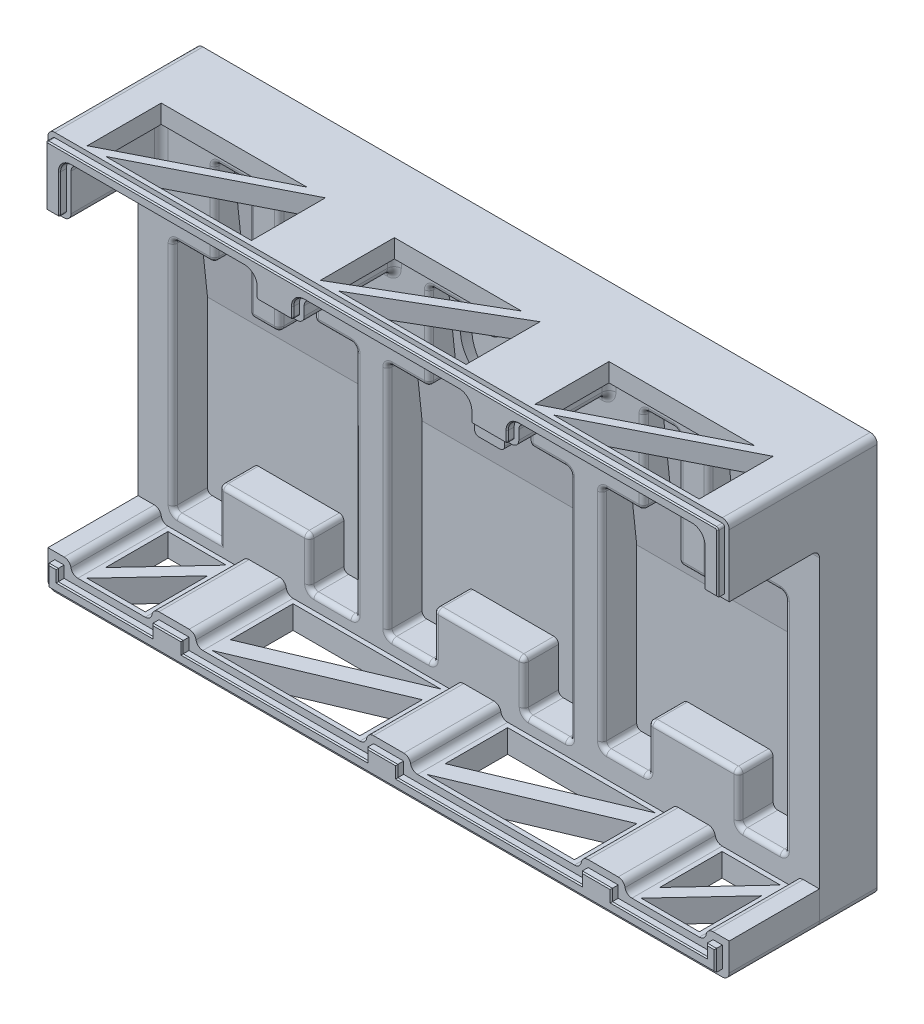
SolidWorks part; units mm, degrees
material "PP generico"
ref_plane "Piano frontale" through (0, 0, 0) normal (0, 0, 1) x (1, 0, 0)
ref_plane "Piano superiore" through (0, 0, 0) normal (0, 1, 0) x (1, 0, 0)
ref_plane "Piano destro" through (0, 0, 0) normal (1, 0, 0) x (0, 0, -1)
sketch "Schizzo1" plane through (0, 0, 0) normal (0, 0, 1) x (1, 0, 0)
  line L1 (-147.3, 86) -> (147.3, 86)
  line L2 (-147.3, 86) -> (-147.3, -86)
  line L3 (-147.3, -86) -> (147.3, -86)
  line L4 (147.3, 86) -> (147.3, -86)
  dimension "D1" = 294.6
  dimension "D2" = 172
  dimension "D3" = 147.3
  dimension "D4" = 86
extrude "Estrusione-Estrusione1" add sketch "Schizzo1" along normal blind 10 contours L1 L4 L3 L2
sketch "Schizzo2" plane through (0, 0, 10) normal (0, 0, 1) x (1, 0, 0)
  line L0 (-73.3, -70) -> (-53.3, -70)
  line L1 (-147.3, 86) -> (147.3, 86)
  line L2 (-147.3, 86) -> (-147.3, -86)
  line L3 (-6.3232, -86) -> (147.3, -86)
  line L4 (147.3, 86) -> (147.3, -86)
  line L9 (-114.3, 70) -> (-99.3, 70)
  line L10 (-132.3, 32) -> (-132.3, -70)
  line L11 (-132.3, -70) -> (-112.3, -70)
  line L12 (-53.3, 32) -> (-53.3, -70)
  line L14 (-39.5, 32) -> (-39.5, -69.8088)
  line L15 (-39.5, -69.8088) -> (-19.5, -69.8088)
  line L16 (39.5, 32) -> (39.5, -69.8088)
  line L18 (53.3, 32) -> (53.3, -65.4933)
  line L19 (53.3, -65.4933) -> (73.3, -65.4933)
  line L20 (132.3, 32) -> (132.3, -65.4933)
  line L21 (-112.3, -49) -> (-73.3, -49)
  line L22 (-112.3, -49) -> (-112.3, -70)
  line L24 (-73.3, -49) -> (-73.3, -70)
  line L25 (19.5, -69.8088) -> (39.5, -69.8088)
  line L26 (-19.5, -48.8088) -> (19.5, -48.8088)
  line L27 (-19.5, -48.8088) -> (-19.5, -69.8088)
  line L29 (19.5, -48.8088) -> (19.5, -69.8088)
  line L30 (73.3, -44.4933) -> (112.3, -44.4933)
  line L31 (73.3, -44.4933) -> (73.3, -65.4933)
  line L33 (112.3, -44.4933) -> (112.3, -65.4933)
  line L34 (112.3, -65.4933) -> (132.3, -65.4933)
  line L35 (-86.3, 70) -> (-71.3, 70)
  line L38 (-132.3, 32) -> (-114.3, 32)
  line L39 (-114.3, 70) -> (-114.3, 32)
  line L42 (-53.3, 32) -> (-71.3, 32)
  line L43 (-71.3, 70) -> (-71.3, 32)
  line L45 (-99.3, 70) -> (-99.3, 20)
  line L46 (-99.3, 20) -> (-86.3, 20)
  line L47 (-86.3, 70) -> (-86.3, 20)
  line L48 (-21.5, 70) -> (-21.5, 32)
  line L49 (-39.5, 32) -> (-21.5, 32)
  line L50 (-21.5, 70) -> (-6.5, 70)
  line L51 (-6.5, 70) -> (-6.5, 20)
  line L52 (6.5, 70) -> (6.5, 20)
  line L53 (6.5, 70) -> (21.5, 70)
  line L54 (21.5, 70) -> (21.5, 32)
  line L55 (39.5, 32) -> (21.5, 32)
  line L56 (-6.5, 20) -> (6.5, 20)
  line L57 (71.3, 70) -> (71.3, 32)
  line L58 (53.3, 32) -> (71.3, 32)
  line L59 (71.3, 70) -> (86.3, 70)
  line L60 (86.3, 70) -> (86.3, 20)
  line L61 (99.3, 70) -> (99.3, 20)
  line L62 (99.3, 70) -> (114.3, 70)
  line L63 (114.3, 70) -> (114.3, 32)
  line L64 (132.3, 32) -> (114.3, 32)
  line L65 (86.3, 20) -> (99.3, 20)
  dimension "D3" = 15
  dimension "D4" = 13.8
  dimension "D5" = 140
  dimension "D6" = 38
  dimension "D7" = 38
  dimension "D8" = 20
  dimension "D9" = 20
  dimension "D10" = 21
  dimension "D11" = 20
  dimension "D12" = 20
  dimension "D13" = 16
  dimension "D16" = 20
  dimension "D17" = 20
  dimension "D18" = 21
  dimension "D19" = 21
  dimension "D20" = 18
  dimension "D21" = 18
  dimension "D22" = 15
  dimension "D23" = 15
  dimension "D24" = 50
  dimension "D25" = 3
extrude "Estrusione-Estrusione2" add sketch "Schizzo2" along normal blind 15
sketch "Schizzo4" plane through (132.3, 0, 0) normal (-1, 0, 0) x (0, 0, 1)
  line L0 (10, 70) -> (10, 3.34)
  line L1 (10, 32) -> (10, -65.4933) construction
  line L2 (10, 3.34) -> (17.12, 70)
  line L4 (17.12, 70) -> (10, 70)
  dimension "D3" = 68.8333
extrude "Estrusione-Estrusione3" add sketch "Schizzo4" along normal up to surface (264.6 mm away) up to face at (-132.3, -19, 17.5)
sketch "Schizzo5" plane through (0, 0, 25) normal (0, 0, 1) x (1, 0, 0)
  line L0 (-147.3, 86) -> (-147.3, 56)
  line L1 (-147.3, 86) -> (-147.3, -86) construction
  line L2 (-147.3, 56) -> (-137.3, 56)
  line L3 (-137.3, 56) -> (-137.3, 78)
  line L4 (-137.3, 78) -> (-56.3, 78)
  line L5 (-56.3, 78) -> (-56.3, 68)
  line L6 (-56.3, 68) -> (-36.5, 68)
  line L7 (-36.5, 68) -> (-36.5, 78)
  line L8 (-36.5, 78) -> (36.5, 78)
  line L9 (36.5, 78) -> (36.5, 68)
  line L10 (36.5, 68) -> (56.3, 68)
  line L11 (56.3, 68) -> (56.3, 78)
  line L12 (56.3, 78) -> (137.3, 78)
  line L13 (137.3, 78) -> (137.3, 56)
  line L14 (137.3, 56) -> (147.3, 56)
  line L15 (147.3, -86) -> (147.3, 86) construction
  line L16 (147.3, 56) -> (147.3, 86)
  line L17 (147.3, 86) -> (-147.3, 86)
  line L18 (-21.5, 70) -> (-21.5, 32) construction
  line L19 (-71.3, 32) -> (-71.3, 70) construction
  line L20 (21.5, 32) -> (21.5, 70) construction
  line L22 (71.3, 70) -> (71.3, 32) construction
  dimension "D1" = 30
  dimension "D2" = 30
  dimension "D3" = 10
  dimension "D4" = 10
  dimension "D5" = 15
  dimension "D6" = 15
  dimension "D7" = 8
  dimension "D8" = 15
  dimension "D9" = 8
  dimension "D10" = 15
  dimension "D11" = 8
extrude "Estrusione-Estrusione4" add sketch "Schizzo5" along normal blind 39
fillet "Raccordo1" radius 3 27 edges at (137.3, 67, 25) (36.5, 73, 25) (56.3, 73, 25) (-36.5, 73, 25) (-56.3, 73, 25) (147.3, 86, 32) (137.3, 78, 44.5) (137.3, 56, 44.5) (142.3, 56, 25) (96.8, 78, 25) (56.3, 78, 44.5) (36.5, 78, 44.5) (36.5, 68, 44.5) (56.3, 68, 44.5) (46.4, 68, 25) (0, 78, 25) (-36.5, 68, 44.5) (-36.5, 78, 44.5) (-46.4, 68, 25) (-56.3, 68, 44.5) (-147.3, 86, 32) (-137.3, 56, 44.5) (-137.3, 78, 44.5) (-96.8, 78, 25) (-142.3, 56, 25) (-137.3, 67, 25) (-56.3, 78, 44.5)
fillet "Raccordo2" radius 2 31 edges at (-114.3, 51, 25) (-123.3, 32, 25) (-53.3, -70, 17.5) (-132.3, -70, 17.5) (-112.3, -49, 17.5) (-73.3, -70, 17.5) (-73.3, -49, 17.5) (-53.3, 32, 19.0306) (-99.3, 70, 21.06) (-86.3, 70, 21.06) (-71.3, 70, 21.06) (-71.3, 32, 19.0306) (-86.3, 20, 18.3897) (-99.3, 20, 18.3897) (-71.3, 51, 25) (-86.3, 45, 25) (-99.3, 45, 25) (-92.8, 20, 25) (-106.8, 70, 25) (-78.8, 70, 25) (-62.3, 32, 25) (-53.3, -19, 25) (-63.3, -70, 25) (-73.3, -59.5, 25) (-92.8, -49, 25) (-112.3, -59.5, 25) (-122.3, -70, 25) (-132.3, -19, 25) (-114.3, 70, 21.06) (-132.3, 32, 19.0306) (-114.3, 32, 19.0306)
fillet "Raccordo4" radius 2 64 edges at (114.3, 51, 25) (106.8, 70, 25) (78.8, 70, 25) (53.3, -16.7467, 25) (132.3, -65.4933, 17.5) (132.3, 32, 19.0306) (86.3, 20, 18.3897) (114.3, 32, 19.0306) (114.3, 70, 21.06) (99.3, 70, 21.06) (86.3, 70, 21.06) (71.3, 51, 25) (71.3, 70, 21.06) (53.3, 32, 19.0306) (73.3, -65.4933, 17.5) (73.3, -44.4933, 17.5) (112.3, -65.4933, 17.5) (132.3, -16.7467, 25) (123.3, 32, 25) (99.3, 45, 25) (86.3, 45, 25) (92.8, 20, 25) (62.3, 32, 25) (92.8, -44.4933, 25) (63.3, -65.4933, 25) (73.3, -54.9933, 25) (112.3, -54.9933, 25) (122.3, -65.4933, 25) (112.3, -44.4933, 17.5) (99.3, 20, 18.3897) (71.3, 32, 19.0306) (53.3, -65.4933, 17.5) (-39.5, -69.8088, 17.5) (19.5, -69.8088, 17.5) (39.5, -69.8088, 17.5) (19.5, -48.8088, 17.5) (-19.5, -48.8088, 17.5) (-19.5, -69.8088, 17.5) (-39.5, 32, 19.0306) (-21.5, 70, 21.06) (6.5, 70, 21.06) (21.5, 70, 21.06) (39.5, 32, 19.0306) (-21.5, 32, 19.0306) (-6.5, 20, 18.3897) (6.5, 20, 18.3897) (21.5, 32, 19.0306) (30.5, 32, 25) (21.5, 51, 25) (6.5, 45, 25) (-21.5, 51, 25) (-30.5, 32, 25) (-6.5, 45, 25) (0, 20, 25) (39.5, -18.9044, 25) (29.5, -69.8088, 25) (19.5, -59.3088, 25) (0, -48.8088, 25) (-19.5, -59.3088, 25) (-39.5, -18.9044, 25) (-29.5, -69.8088, 25) (-14, 70, 25) (14, 70, 25) (-6.5, 70, 21.06)
sketch "Schizzo8" plane through (0, 0, 25) normal (0, 0, 1) x (1, 0, 0)
  line L0 (-147.3, -86) -> (-147.3, -71)
  line L1 (-147.3, 53) -> (-147.3, -86) construction
  line L2 (-147.3, -71) -> (-137.3, -71)
  line L3 (-137.3, -71) -> (-137.3, -76)
  line L4 (-137.3, -76) -> (-102.3, -76)
  line L5 (-102.3, -76) -> (-102.3, -71)
  line L6 (-102.3, -71) -> (-83.3, -71)
  line L7 (-83.3, -71) -> (-83.3, -76)
  line L8 (-83.3, -76) -> (-9.5, -76)
  line L9 (-9.5, -76) -> (-9.5, -71)
  line L10 (-9.5, -71) -> (9.5, -71)
  line L11 (9.5, -71) -> (9.5, -76)
  line L12 (9.5, -76) -> (83.3, -76)
  line L13 (83.3, -76) -> (83.3, -71)
  line L14 (83.3, -71) -> (102.3, -71)
  line L15 (102.3, -71) -> (102.3, -76)
  line L16 (102.3, -76) -> (137.3, -76)
  line L17 (137.3, -76) -> (137.3, -71)
  line L18 (137.3, -71) -> (147.3, -71)
  line L19 (147.3, -86) -> (147.3, 53) construction
  line L20 (147.3, -71) -> (147.3, -86)
  line L21 (147.3, -86) -> (-147.3, -86)
  line L22 (-110.3, -51) -> (-110.3, -72) construction
  line L23 (-75.3, -68) -> (-75.3, -51) construction
  line L26 (75.3, -46.4933) -> (75.3, -63.4933) construction
  line L27 (110.3, -63.4933) -> (110.3, -46.4933) construction
  line L28 (-17.5, -50.8088) -> (-17.5, -67.8088) construction
  line L29 (17.5, -67.8088) -> (17.5, -50.8088) construction
  dimension "D1" = 10
  dimension "D2" = 10
  dimension "D3" = 15
  dimension "D4" = 15
  dimension "D5" = 15
  dimension "D6" = 15
  dimension "D7" = 15
  dimension "D8" = 8
  dimension "D9" = 8
  dimension "D10" = 8
  dimension "D11" = 8
  dimension "D12" = 8
  dimension "D13" = 8
  dimension "D14" = 10
  dimension "D15" = 10
  dimension "D16" = 10
  dimension "D17" = 10
extrude "Estrusione-Estrusione5" add sketch "Schizzo8" along normal up to surface (39 mm away) up to face at (0, 71.8414, 64)
fillet "Raccordo8" radius 3 2 edges at (147.3, -86, 12.5) (-147.3, -86, 12.5)
sketch "Schizzo10" plane through (0, 0, 64) normal (0, 0, 1) x (1, 0, 0)
  line L16 (-38.5, 71) -> (-38.5, 75)
  line L17 (-38.5, 71) -> (-38.5, 75)
  line L18 (140.3, -74) -> (140.3, -79)
  line L19 (140.3, -74) -> (140.3, -79)
  line L20 (99.3, -79) -> (99.3, -74)
  line L21 (99.3, -79) -> (99.3, -74)
  line L22 (86.3, -74) -> (86.3, -79)
  line L23 (86.3, -74) -> (86.3, -79)
  line L24 (6.5, -79) -> (6.5, -74)
  line L25 (6.5, -79) -> (6.5, -74)
  line L26 (-6.5, -74) -> (-6.5, -79)
  line L27 (-6.5, -74) -> (-6.5, -79)
  line L28 (-86.3, -79) -> (-86.3, -74)
  line L29 (-86.3, -79) -> (-86.3, -74)
  line L30 (38.5, 75) -> (38.5, 71)
  line L31 (38.5, 75) -> (38.5, 71)
  line L32 (-99.3, -74) -> (-99.3, -79)
  line L33 (-99.3, -74) -> (-99.3, -79)
  line L34 (-140.3, -79) -> (-140.3, -74)
  line L35 (-140.3, -79) -> (-140.3, -74)
  line L72 (-144.3, -83) -> (144.3, -83)
  line L73 (144.3, -83) -> (144.3, -74)
  line L74 (144.3, -74) -> (140.3, -74)
  line L75 (140.3, -79) -> (99.3, -79)
  line L76 (99.3, -74) -> (86.3, -74)
  line L77 (86.3, -79) -> (6.5, -79)
  line L78 (6.5, -74) -> (-6.5, -74)
  line L79 (-6.5, -79) -> (-86.3, -79)
  line L80 (-86.3, -74) -> (-99.3, -74)
  line L81 (-99.3, -79) -> (-140.3, -79)
  line L82 (-140.3, -74) -> (-144.3, -74)
  line L83 (-144.3, -74) -> (-144.3, -83)
  line L84 (-144.3, -83) -> (144.3, -83)
  line L85 (144.3, -83) -> (144.3, -74)
  line L86 (144.3, -74) -> (140.3, -74)
  line L87 (140.3, -79) -> (99.3, -79)
  line L88 (99.3, -74) -> (86.3, -74)
  line L89 (86.3, -79) -> (6.5, -79)
  line L90 (6.5, -74) -> (-6.5, -74)
  line L91 (-6.5, -79) -> (-86.3, -79)
  line L92 (-86.3, -74) -> (-99.3, -74)
  line L93 (-99.3, -79) -> (-140.3, -79)
  line L94 (-140.3, -74) -> (-144.3, -74)
  line L95 (-144.3, -74) -> (-144.3, -83)
  line L100 (140.3, 58) -> (145.3, 58)
  line L101 (145.3, 58) -> (145.3, 83)
  line L102 (144.3, 84) -> (-144.3, 84)
  line L103 (-145.3, 83) -> (-145.3, 58)
  line L104 (-145.3, 58) -> (-140.3, 58)
  line L105 (-139.3, 59) -> (-139.3, 75)
  line L106 (-134.3, 80) -> (-59.3, 80)
  line L107 (-54.3, 75) -> (-54.3, 71)
  line L108 (-53.3, 70) -> (-39.5, 70)
  line L110 (-33.5, 80) -> (33.5, 80)
  line L112 (39.5, 70) -> (53.3, 70)
  line L113 (54.3, 71) -> (54.3, 75)
  line L114 (59.3, 80) -> (134.3, 80)
  line L115 (139.3, 75) -> (139.3, 59)
  line L116 (140.3, 58) -> (145.3, 58)
  line L117 (145.3, 58) -> (145.3, 83)
  line L118 (144.3, 84) -> (-144.3, 84)
  line L119 (-145.3, 83) -> (-145.3, 58)
  line L120 (-145.3, 58) -> (-140.3, 58)
  line L121 (-139.3, 59) -> (-139.3, 75)
  line L122 (-134.3, 80) -> (-59.3, 80)
  line L123 (-54.3, 75) -> (-54.3, 71)
  line L124 (-53.3, 70) -> (-39.5, 70)
  line L126 (-33.5, 80) -> (33.5, 80)
  line L128 (39.5, 70) -> (53.3, 70)
  line L129 (54.3, 71) -> (54.3, 75)
  line L130 (59.3, 80) -> (134.3, 80)
  line L131 (139.3, 75) -> (139.3, 59)
  arc A85 (145.3, 83) -> (144.3, 84) centre (144.3, 83) ccw
  arc A86 (-144.3, 84) -> (-145.3, 83) centre (-144.3, 83) ccw
  arc A104 (-140.3, 58) -> (-139.3, 59) centre (-140.3, 59) ccw
  arc A105 (-134.3, 80) -> (-139.3, 75) centre (-134.3, 75) ccw
  arc A106 (-54.3, 75) -> (-59.3, 80) centre (-59.3, 75) ccw
  arc A107 (-54.3, 71) -> (-53.3, 70) centre (-53.3, 71) ccw
  arc A108 (-39.5, 70) -> (-38.5, 71) centre (-39.5, 71) ccw
  arc A109 (-33.5, 80) -> (-38.5, 75) centre (-33.5, 75) ccw
  arc A110 (38.5, 75) -> (33.5, 80) centre (33.5, 75) ccw
  arc A111 (38.5, 71) -> (39.5, 70) centre (39.5, 71) ccw
  arc A112 (53.3, 70) -> (54.3, 71) centre (53.3, 71) ccw
  arc A113 (59.3, 80) -> (54.3, 75) centre (59.3, 75) ccw
  arc A114 (139.3, 75) -> (134.3, 80) centre (134.3, 75) ccw
  arc A115 (139.3, 59) -> (140.3, 58) centre (140.3, 59) ccw
  arc A117 (145.3, 83) -> (144.3, 84) centre (144.3, 83) ccw
  arc A118 (-144.3, 84) -> (-145.3, 83) centre (-144.3, 83) ccw
  arc A120 (-140.3, 58) -> (-139.3, 59) centre (-140.3, 59) ccw
  arc A121 (-134.3, 80) -> (-139.3, 75) centre (-134.3, 75) ccw
  arc A122 (-54.3, 75) -> (-59.3, 80) centre (-59.3, 75) ccw
  arc A123 (-54.3, 71) -> (-53.3, 70) centre (-53.3, 71) ccw
  arc A124 (-39.5, 70) -> (-38.5, 71) centre (-39.5, 71) ccw
  arc A125 (-33.5, 80) -> (-38.5, 75) centre (-33.5, 75) ccw
  arc A126 (38.5, 75) -> (33.5, 80) centre (33.5, 75) ccw
  arc A127 (38.5, 71) -> (39.5, 70) centre (39.5, 71) ccw
  arc A128 (53.3, 70) -> (54.3, 71) centre (53.3, 71) ccw
  arc A129 (59.3, 80) -> (54.3, 75) centre (59.3, 75) ccw
  arc A130 (139.3, 75) -> (134.3, 80) centre (134.3, 75) ccw
  arc A131 (139.3, 59) -> (140.3, 58) centre (140.3, 59) ccw
  dimension "D1" = 2
  dimension "D2" = 3
extrude "Estrusione-Estrusione6" add sketch "Schizzo10" along normal blind 3
sketch "Schizzo11" plane through (0, 0, 0) normal (0, 0, 1) x (1, 0, 0)
  line L84 (-144.3, -83) -> (144.3, -83)
  line L85 (144.3, -83) -> (144.3, -74)
  line L86 (144.3, -74) -> (140.3, -74)
  line L87 (134.3839, -79) -> (107.2161, -79)
  line L88 (101.3, -74) -> (84.3, -74)
  line L89 (78.3839, -79) -> (14.4161, -79)
  line L90 (8.5, -74) -> (-8.5, -74)
  line L91 (-14.4161, -79) -> (-78.3839, -79)
  line L92 (-84.3, -74) -> (-101.3, -74)
  line L93 (-107.2161, -79) -> (-134.3839, -79)
  line L94 (-140.3, -74) -> (-144.3, -74)
  line L95 (-144.3, -74) -> (-144.3, -83)
  line L116 (140.3, 58) -> (144.3, 58)
  line L117 (145.3, 59) -> (145.3, 83)
  line L118 (144.3, 84) -> (-144.3, 84)
  line L119 (-145.3, 83) -> (-145.3, 59)
  line L120 (-144.3, 58) -> (-140.3, 58)
  line L121 (-139.3, 59) -> (-139.3, 75)
  line L122 (-134.3, 80) -> (-59.3, 80)
  line L123 (-54.3, 75) -> (-54.3, 71)
  line L124 (-53.3, 70) -> (-39.5, 70)
  line L125 (-38.5, 71) -> (-38.5, 75)
  line L126 (-33.5, 80) -> (33.5, 80)
  line L127 (38.5, 75) -> (38.5, 71)
  line L128 (39.5, 70) -> (53.3, 70)
  line L129 (54.3, 71) -> (54.3, 75)
  line L130 (59.3, 80) -> (134.3, 80)
  line L131 (139.3, 75) -> (139.3, 59)
  arc A96 (134.3839, -79) -> (140.3, -74) centre (134.3839, -73) ccw
  arc A97 (101.3, -74) -> (107.2161, -79) centre (107.2161, -73) ccw
  arc A98 (78.3839, -79) -> (84.3, -74) centre (78.3839, -73) ccw
  arc A99 (8.5, -74) -> (14.4161, -79) centre (14.4161, -73) ccw
  arc A100 (-14.4161, -79) -> (-8.5, -74) centre (-14.4161, -73) ccw
  arc A101 (-84.3, -74) -> (-78.3839, -79) centre (-78.3839, -73) ccw
  arc A102 (-107.2161, -79) -> (-101.3, -74) centre (-107.2161, -73) ccw
  arc A103 (-140.3, -74) -> (-134.3839, -79) centre (-134.3839, -73) ccw
  arc A116 (144.3, 58) -> (145.3, 59) centre (144.3, 59) ccw
  arc A117 (145.3, 83) -> (144.3, 84) centre (144.3, 83) ccw
  arc A118 (-144.3, 84) -> (-145.3, 83) centre (-144.3, 83) ccw
  arc A119 (-145.3, 59) -> (-144.3, 58) centre (-144.3, 59) ccw
  arc A120 (-140.3, 58) -> (-139.3, 59) centre (-140.3, 59) ccw
  arc A121 (-134.3, 80) -> (-139.3, 75) centre (-134.3, 75) ccw
  arc A122 (-54.3, 75) -> (-59.3, 80) centre (-59.3, 75) ccw
  arc A123 (-54.3, 71) -> (-53.3, 70) centre (-53.3, 71) ccw
  arc A124 (-39.5, 70) -> (-38.5, 71) centre (-39.5, 71) ccw
  arc A125 (-33.5, 80) -> (-38.5, 75) centre (-33.5, 75) ccw
  arc A126 (38.5, 75) -> (33.5, 80) centre (33.5, 75) ccw
  arc A127 (38.5, 71) -> (39.5, 70) centre (39.5, 71) ccw
  arc A128 (53.3, 70) -> (54.3, 71) centre (53.3, 71) ccw
  arc A129 (59.3, 80) -> (54.3, 75) centre (59.3, 75) ccw
  arc A130 (139.3, 75) -> (134.3, 80) centre (134.3, 75) ccw
  arc A131 (139.3, 59) -> (140.3, 58) centre (140.3, 59) ccw
extrude "Taglio-Estrusione1" cut sketch "Schizzo11" along normal blind 4
fillet "Raccordo9" radius 3 4 edges at (9.5, -76, 44.5) (-83.3, -76, 44.5) (-102.3, -71, 44.5) (-9.5, -71, 44.5)
fillet "Raccordo10" radius 3 4 edges at (-9.5, -76, 44.5) (-137.3, -71, 44.5) (-83.3, -71, 44.5) (-102.3, -76, 44.5)
fillet "Raccordo11" radius 3 2 edges at (-137.3, -76, 44.5) (137.3, -71, 44.5)
fillet "Raccordo12" radius 3 2 edges at (137.3, -76, 44.5) (102.3, -71, 44.5)
fillet "Raccordo13" radius 3 3 edges at (102.3, -76, 44.5) (9.5, -71, 44.5) (83.3, -71, 44.5)
fillet "Raccordo14" radius 3 2 edges at (-147.3, -86, 44.5) (147.3, -86, 44.5)
chamfer "Smusso1" distance 0.5 angle 45 20 edges at (144.3, -78.5, 67) (0, -83, 67) (-144.3, -78.5, 67) (-142.3, -74, 67) (-140.3, -76.5, 67) (-119.8, -79, 67) (-99.3, -76.5, 67) (-92.8, -74, 67) (-86.3, -76.5, 67) (-46.4, -79, 67) (-6.5, -76.5, 67) (0, -74, 67) (6.5, -76.5, 67) (46.4, -79, 67) (86.3, -76.5, 67) (92.8, -74, 67) (99.3, -76.5, 67) (119.8, -79, 67) (140.3, -76.5, 67) (142.3, -74, 67)
chamfer "Smusso2" distance 0.5 angle 45 30 edges at (142.8, 58, 67) (139.5929, 58.2929, 67) (139.3, 67, 67) (137.8355, 78.5355, 67) (96.8, 80, 67) (55.7645, 78.5355, 67) (54.3, 73, 67) (54.0071, 70.2929, 67) (46.4, 70, 67) (38.7929, 70.2929, 67) (38.5, 73, 67) (37.0355, 78.5355, 67) (0, 80, 67) (-37.0355, 78.5355, 67) (-38.5, 73, 67) (-38.7929, 70.2929, 67) (-46.4, 70, 67) (-54.0071, 70.2929, 67) (-54.3, 73, 67) (-55.7645, 78.5355, 67) (-96.8, 80, 67) (-137.8355, 78.5355, 67) (-139.3, 67, 67) (-139.5929, 58.2929, 67) (-142.8, 58, 67) (-145.3, 70.5, 67) (-145.0071, 83.7071, 67) (0, 84, 67) (145.0071, 83.7071, 67) (145.3, 70.5, 67)
sketch "Schizzo12" plane through (0, 78, 0) normal (0, -1, 0) x (1, 0, 0)
  line L0 (-132.3, 30) -> (-132.3, 62)
  line L1 (-132.3, 62) -> (-69.3, 30)
  line L2 (-69.3, 30) -> (-132.3, 30)
  line L3 (-134.3, 64) -> (-134.3, 28) construction
  line L4 (-134.3, 28) -> (-59.3, 28) construction
  line L5 (-124.3, 62) -> (-61.3, 62)
  line L6 (-61.3, 62) -> (-61.3, 30)
  line L7 (-61.3, 30) -> (-124.3, 62)
  line L8 (-134.3, 64) -> (-59.3, 64) construction
  line L9 (-59.3, 28) -> (-59.3, 64) construction
  line L10 (132.3, 62) -> (132.3, 30)
  line L11 (132.3, 30) -> (69.3, 62)
  line L12 (61.3, 62) -> (124.3, 30)
  line L13 (124.3, 30) -> (61.3, 30)
  line L14 (61.3, 30) -> (61.3, 62)
  line L15 (69.3, 62) -> (132.3, 62)
  line L16 (59.3, 64) -> (59.3, 28) construction
  line L17 (-33.5, 28) -> (33.5, 28) construction
  line L18 (-31.5, 30) -> (23.5, 30)
  line L19 (23.5, 30) -> (-31.5, 62)
  line L20 (-31.5, 62) -> (-31.5, 30)
  line L21 (-23.5, 62) -> (31.5, 62)
  line L22 (31.5, 62) -> (31.5, 30)
  line L23 (31.5, 30) -> (-23.5, 62)
  line L24 (-33.5, 64) -> (-33.5, 28) construction
  line L25 (33.5, 28) -> (33.5, 64) construction
  line L27 (-33.5, 64) -> (33.5, 64) construction
  point P32 (0, 0)
  point P33 (0, 0)
  point P34 (0, 0)
  point P35 (21.0765, 30)
  point P38 (-31.5, 53.156)
  point P39 (0, 0)
  dimension "D1" = 2
  dimension "D2" = 2
  dimension "D3" = 2
  dimension "D4" = 2
  dimension "D5" = 2
  dimension "D6" = 2
  dimension "D7" = 10
  dimension "D8" = 10
  dimension "D10" = 2
  dimension "D11" = 2
  dimension "D12" = 2
  dimension "D13" = 10
  dimension "D14" = 10
  dimension "D15" = 2
  dimension "D16" = 2
  dimension "D9" = 2
extrude "Taglio-Estrusione2" cut sketch "Schizzo12" against normal blind 10
sketch "Schizzo14" plane through (0, -76, 0) normal (0, 1, 0) x (1, 0, 0)
  line L0 (-78.3, -27) -> (-14.4161, -27)
  line L1 (-14.4161, -27) -> (-78.3, -54)
  line L2 (-78.3, -54) -> (-78.3, -27)
  line L3 (-78.3, -62) -> (-14.4161, -35)
  line L4 (-14.4161, -35) -> (-14.4161, -62)
  line L5 (-14.4161, -62) -> (-78.3, -62)
  line L7 (-6.5, -64) -> (-86.3, -64) construction
  line L8 (-12.4161, -25) -> (-80.3, -25) construction
  line L9 (-12.4161, -64) -> (-12.4161, -25) construction
  line L10 (-144.3, -25) -> (144.3, -25) construction
  line L11 (-80.3, -25) -> (-80.3, -64) construction
  line L12 (78.3839, -62) -> (14.5, -62)
  line L13 (78.3839, -35) -> (78.3839, -62)
  line L14 (14.5, -62) -> (78.3839, -35)
  line L15 (78.3839, -27) -> (14.5, -54)
  line L16 (14.5, -54) -> (14.5, -27)
  line L17 (14.5, -27) -> (78.3839, -27)
  line L20 (12.5, -25) -> (12.5, -64) construction
  line L21 (107.2161, -27) -> (132.3839, -27)
  line L22 (132.3839, -27) -> (107.2161, -54)
  line L23 (107.2161, -54) -> (107.2161, -27)
  line L24 (132.3839, -35) -> (132.3839, -62)
  line L25 (132.3839, -62) -> (107.2161, -62)
  line L26 (107.2161, -62) -> (132.3839, -35)
  line L27 (105.2161, -25) -> (105.2161, -64) construction
  line L28 (134.3839, -64) -> (134.3839, -25) construction
  line L29 (134.3839, -64) -> (105.2161, -64) construction
  line L30 (134.3839, -25) -> (105.2161, -25) construction
  line L31 (-132.3839, -27) -> (-107.2161, -27)
  line L32 (-132.3839, -54) -> (-132.3839, -27)
  line L33 (-107.2161, -27) -> (-132.3839, -54)
  line L34 (-132.3839, -62) -> (-107.2161, -35)
  line L35 (-107.2161, -62) -> (-132.3839, -62)
  line L36 (-107.2161, -35) -> (-107.2161, -62)
  line L37 (-134.3839, -25) -> (-134.3839, -64) construction
  dimension "D1" = 2
  dimension "D2" = 2
  dimension "D3" = 2
  dimension "D4" = 10
  dimension "D5" = 2
  dimension "D6" = 2
  dimension "D7" = 2
  dimension "D9" = 2
  dimension "D10" = 2
  dimension "D11" = 2
  dimension "D12" = 2
  dimension "D13" = 10
  dimension "D14" = 10
  dimension "D15" = 2
  dimension "D17" = 2
  dimension "D8" = 2
  dimension "D16" = 2
extrude "Taglio-Estrusione3" cut sketch "Schizzo14" against normal blind 10
fillet "Raccordo15" radius 3 1 edges at (83.3, -76, 44.5)
sketch "Schizzo15" plane through (0, 20, 0) normal (0, -1, 0) x (1, 0, 0)
  line L1 (-8.824, 26.8346) -> (9.6819, 26.8346)
  line L2 (-8.824, 26.8346) -> (-8.824, 20.3575)
  line L3 (-8.824, 20.3575) -> (9.6819, 20.3575)
  line L4 (9.6819, 26.8346) -> (9.6819, 20.3575)
extrude "Taglio-Estrusione4" cut sketch "Schizzo15" against normal blind 37
sketch "Schizzo16" plane through (0, 0, 20.3575) normal (0, 0, 1) x (1, 0, 0)
  line L1 (-4.5, 20) -> (4.5, 20) construction
  line L2 (-6.5, 22) -> (-6.5, 57) construction
  circle A0 centre (-0.5, 48.5) radius 17.5
  dimension "D1" = 35
  dimension "D2" = 28.5
  dimension "D3" = 6
extrude "Taglio-Estrusione5" cut sketch "Schizzo16" against normal up to surface (10.3575 mm away) and the other way blind 37 up to face at (0, -53.1324, 10)
